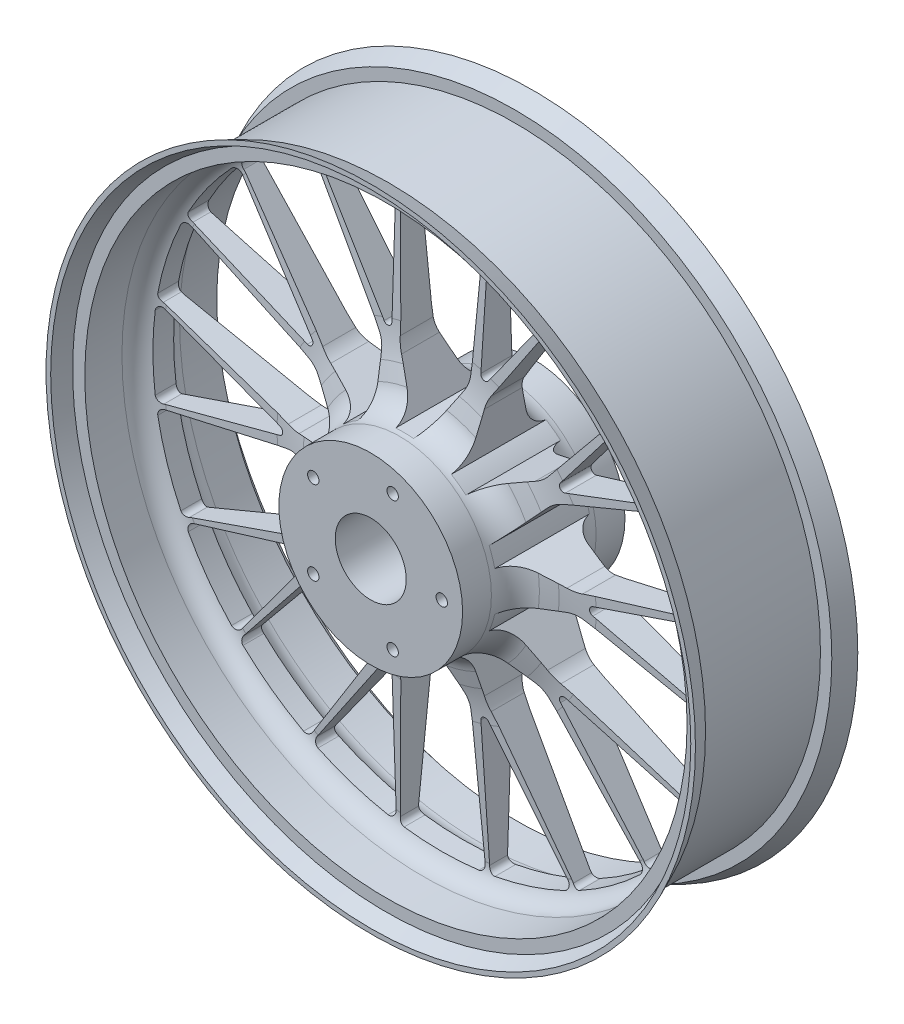
SolidWorks part; units mm, degrees
material "7050-T7651"
ref_plane "Front Plane" through (0, 0, 0) normal (0, 0, 1) x (1, 0, 0)
ref_plane "Top Plane" through (0, 0, 0) normal (0, 1, 0) x (1, 0, 0)
ref_plane "Right Plane" through (0, 0, 0) normal (1, 0, 0) x (0, 0, -1)
sketch "Sketch1" plane through (0, 0, 0) normal (0, 0, 1) x (1, 0, 0)
  line L0 (0, 0) -> (0, 203.2) construction
  line L1 (-29.8081, 197.311) -> (-24.756, 100.9121)
  line L2 (-22.1039, 91.9588) -> (-6.3592, 64.6882)
  line L3 (91.8613, 177.1487) -> (39.2866, 96.1908)
  line L4 (22.1039, 91.9588) -> (6.3592, 64.6882)
  line L5 (29.8081, 197.311) -> (24.756, 100.9121)
  line L6 (0, 0) -> (-75.5575, 232.5421) construction
  line L7 (-31.3013, 105.6196) -> (-32.8759, 195.8269)
  line L8 (-36.7583, 103.8465) -> (-88.471, 177.7703)
  line L9 (36.1696, 87.3886) -> (32.878, 56.0717)
  line L10 (71.9345, 61.4039) -> (43.1675, 48.596)
  line L11 (140.0918, 142.1072) -> (79.3427, 67.0884)
  line L12 (36.7583, 103.8465) -> (88.507, 177.7513)
  line L13 (31.3013, 105.6196) -> (32.9162, 195.8211)
  line L14 (0, 0) -> (119.438, 164.3923) construction
  line L15 (0, 0) -> (75.5575, 232.5421) construction
  line L16 (178.4427, 89.3216) -> (88.3231, 54.7279)
  line L17 (80.6276, 49.4389) -> (59.557, 26.0377)
  line L18 (94.2886, 7.3948) -> (63.4872, 13.9418)
  line L19 (196.8651, 32.6233) -> (103.6232, 7.6392)
  line L20 (90.7776, 62.4076) -> (176.0833, 91.7807)
  line L21 (87.405, 67.0496) -> (141.7305, 139.075)
  line L22 (0, 0) -> (193.2547, 62.7923) construction
  line L23 (0, 0) -> (197.8121, 143.7189) construction
  line L24 (196.8651, -32.6233) -> (103.6232, -7.6392)
  line L25 (94.2886, -7.3948) -> (63.4872, -13.9418)
  line L26 (80.6276, -49.4389) -> (59.557, -26.0377)
  line L27 (178.4427, -89.3216) -> (88.3231, -54.7279)
  line L28 (110.1229, -2.8689) -> (196.4017, -29.247)
  line L29 (110.1229, 2.8689) -> (196.4086, 29.2069)
  line L30 (0, 0) -> (193.2547, -62.7923) construction
  line L31 (0, 0) -> (244.5092, 0) construction
  line L32 (140.0918, -142.1072) -> (79.3427, -67.0884)
  line L33 (71.9345, -61.4039) -> (43.1675, -48.596)
  line L34 (36.1696, -87.3886) -> (32.878, -56.0717)
  line L35 (91.8613, -177.1487) -> (39.2866, -96.1908)
  line L36 (87.405, -67.0496) -> (141.7014, -139.1033)
  line L37 (90.7776, -62.4076) -> (176.0653, -91.8172)
  line L38 (0, 0) -> (119.438, -164.3923) construction
  line L39 (0, 0) -> (197.8121, -143.7189) construction
  line L40 (29.8081, -197.311) -> (24.756, -100.9121)
  line L41 (22.1039, -91.9588) -> (6.3592, -64.6882)
  line L42 (-22.1039, -91.9588) -> (-6.3592, -64.6882)
  line L43 (-29.8081, -197.311) -> (-24.756, -100.9121)
  line L44 (31.3013, -105.6196) -> (32.8759, -195.8269)
  line L45 (36.7583, -103.8465) -> (88.471, -177.7703)
  line L46 (0, 0) -> (0, -203.2) construction
  line L47 (0, 0) -> (75.5575, -232.5421) construction
  line L48 (-91.8613, -177.1487) -> (-39.2866, -96.1908)
  line L49 (-36.1696, -87.3886) -> (-32.878, -56.0717)
  line L50 (-71.9345, -61.4039) -> (-43.1675, -48.596)
  line L51 (-140.0918, -142.1072) -> (-79.3427, -67.0884)
  line L52 (-36.7583, -103.8465) -> (-88.507, -177.7513)
  line L53 (-31.3013, -105.6196) -> (-32.9162, -195.8211)
  line L54 (0, 0) -> (-119.438, -164.3923) construction
  line L55 (0, 0) -> (-75.5575, -232.5421) construction
  line L56 (-178.4427, -89.3216) -> (-88.3231, -54.7279)
  line L57 (-80.6276, -49.4389) -> (-59.557, -26.0377)
  line L58 (-94.2886, -7.3948) -> (-63.4872, -13.9418)
  line L59 (-196.8651, -32.6233) -> (-103.6232, -7.6392)
  line L60 (-90.7776, -62.4076) -> (-176.0833, -91.7807)
  line L61 (-87.405, -67.0496) -> (-141.7305, -139.075)
  line L62 (0, 0) -> (-193.2547, -62.7923) construction
  line L63 (0, 0) -> (-197.8121, -143.7189) construction
  line L64 (-196.8651, 32.6233) -> (-103.6232, 7.6392)
  line L65 (-94.2886, 7.3948) -> (-63.4872, 13.9418)
  line L66 (-80.6276, 49.4389) -> (-59.557, 26.0377)
  line L67 (-178.4427, 89.3216) -> (-88.3231, 54.7279)
  line L68 (-110.1229, 2.8689) -> (-196.4017, 29.247)
  line L69 (-110.1229, -2.8689) -> (-196.4086, -29.2069)
  line L70 (0, 0) -> (-193.2547, 62.7923) construction
  line L71 (0, 0) -> (-244.5092, 0) construction
  line L72 (-140.0918, 142.1072) -> (-79.3427, 67.0884)
  line L73 (-71.9345, 61.4039) -> (-43.1675, 48.596)
  line L74 (-36.1696, 87.3886) -> (-32.878, 56.0717)
  line L75 (-91.8613, 177.1487) -> (-39.2866, 96.1908)
  line L76 (-87.405, 67.0496) -> (-141.7014, 139.1033)
  line L77 (-90.7776, 62.4076) -> (-176.0653, 91.8172)
  line L78 (0, 0) -> (-119.438, 164.3923) construction
  line L79 (0, 0) -> (-197.8121, 143.7189) construction
  circle A0 centre (0, 0) radius 25
  arc A1 (26.3319, 201.4867) -> (-26.3319, 201.4867) centre (0, 0) ccw
  arc A2 (6.3592, 64.6882) -> (-6.3592, 64.6882) centre (0, 0) ccw
  arc A3 (-31.3013, 105.6196) -> (-33.3738, 102.7141) centre (-34.3009, 105.5673) cw
  arc A4 (-36.7583, 103.8465) -> (-33.3738, 102.7141) centre (-34.3009, 105.5673) ccw
  arc A5 (22.1039, 91.9588) -> (24.756, 100.9121) centre (4.7834, 101.9588) ccw
  arc A6 (-24.756, 100.9121) -> (-22.1039, 91.9588) centre (-4.7834, 101.9588) ccw
  arc A7 (-37.6158, 199.688) -> (-86.9041, 183.6788) centre (0, 0) ccw
  arc A8 (29.8081, 197.311) -> (26.3319, 201.4867) centre (25.8136, 197.5204) ccw
  arc A9 (-29.8081, 197.311) -> (-26.3319, 201.4867) centre (-25.8136, 197.5204) cw
  arc A10 (-32.8759, 195.8269) -> (-37.6158, 199.688) centre (-36.8753, 195.7571) ccw
  arc A11 (-88.471, 177.7703) -> (-86.9041, 183.6788) centre (-85.1934, 180.0631) cw
  arc A12 (139.7338, 147.5286) -> (97.1279, 178.4836) centre (0, 0) ccw
  arc A13 (43.1675, 48.596) -> (32.878, 56.0717) centre (0, 0) ccw
  arc A14 (36.7583, 103.8465) -> (33.3738, 102.7141) centre (34.3009, 105.5673) cw
  arc A15 (31.3013, 105.6196) -> (33.3738, 102.7141) centre (34.3009, 105.5673) ccw
  arc A16 (71.9345, 61.4039) -> (79.3427, 67.0884) centre (63.7998, 79.6748) ccw
  arc A17 (39.2866, 96.1908) -> (36.1696, 87.3886) centre (56.06, 85.2981) ccw
  arc A18 (86.9419, 183.661) -> (37.6568, 199.6803) centre (0, 0) ccw
  arc A19 (140.0918, 142.1072) -> (139.7338, 147.5286) centre (136.9832, 144.6245) ccw
  arc A20 (91.8613, 177.1487) -> (97.1279, 178.4836) centre (95.216, 174.9702) cw
  arc A21 (88.507, 177.7513) -> (86.9419, 183.661) centre (85.2304, 180.0456) ccw
  arc A22 (32.9162, 195.8211) -> (37.6568, 199.6803) centre (36.9156, 195.7495) cw
  arc A23 (199.7622, 37.2197) -> (183.4882, 87.3059) centre (0, 0) ccw
  arc A24 (63.4872, 13.9418) -> (59.557, 26.0377) centre (0, 0) ccw
  arc A25 (90.7776, 62.4076) -> (87.3738, 63.4808) centre (89.8009, 65.2442) cw
  arc A26 (87.405, 67.0496) -> (87.3738, 63.4808) centre (89.8009, 65.2442) ccw
  arc A27 (94.2886, 7.3948) -> (103.6232, 7.6392) centre (98.4468, 26.9577) ccw
  arc A28 (88.3231, 54.7279) -> (80.6276, 49.4389) centre (95.4905, 36.0563) ccw
  arc A29 (178.2906, 97.4817) -> (147.8341, 139.4106) centre (0, 0) ccw
  arc A30 (196.8651, 32.6233) -> (199.7622, 37.2197) centre (195.8299, 36.487) ccw
  arc A31 (178.4427, 89.3216) -> (183.4882, 87.3059) centre (179.8762, 85.5873) cw
  arc A32 (176.0833, 91.7807) -> (178.2906, 97.4817) centre (174.781, 95.5628) ccw
  arc A33 (141.7305, 139.075) -> (147.8341, 139.4106) centre (144.924, 136.6663) cw
  arc A34 (183.4882, -87.3059) -> (199.7622, -37.2197) centre (0, 0) ccw
  arc A35 (59.557, -26.0377) -> (63.4872, -13.9418) centre (0, 0) ccw
  arc A36 (110.1229, -2.8689) -> (108, 0) centre (111, 0) cw
  arc A37 (110.1229, 2.8689) -> (108, 0) centre (111, 0) ccw
  arc A38 (80.6276, -49.4389) -> (88.3231, -54.7279) centre (95.4905, -36.0563) ccw
  arc A39 (103.6232, -7.6392) -> (94.2886, -7.3948) centre (98.4468, -26.9577) ccw
  arc A40 (201.5385, -25.9323) -> (201.5438, 25.8908) centre (0, 0) ccw
  arc A41 (178.4427, -89.3216) -> (183.4882, -87.3059) centre (179.8762, -85.5873) ccw
  arc A42 (196.8651, -32.6233) -> (199.7622, -37.2197) centre (195.8299, -36.487) cw
  arc A43 (196.4017, -29.247) -> (201.5385, -25.9323) centre (197.5712, -25.4218) ccw
  arc A44 (196.4086, 29.2069) -> (201.5438, 25.8908) centre (197.5764, 25.3812) cw
  arc A45 (97.1279, -178.4836) -> (139.7338, -147.5286) centre (0, 0) ccw
  arc A46 (32.878, -56.0717) -> (43.1675, -48.596) centre (0, 0) ccw
  arc A47 (87.405, -67.0496) -> (87.3738, -63.4808) centre (89.8009, -65.2442) cw
  arc A48 (90.7776, -62.4076) -> (87.3738, -63.4808) centre (89.8009, -65.2442) ccw
  arc A49 (36.1696, -87.3886) -> (39.2866, -96.1908) centre (56.06, -85.2981) ccw
  arc A50 (79.3427, -67.0884) -> (71.9345, -61.4039) centre (63.7998, -79.6748) ccw
  arc A51 (147.8055, -139.441) -> (178.2706, -97.5184) centre (0, 0) ccw
  arc A52 (91.8613, -177.1487) -> (97.1279, -178.4836) centre (95.216, -174.9702) ccw
  arc A53 (140.0918, -142.1072) -> (139.7338, -147.5286) centre (136.9832, -144.6245) cw
  arc A54 (141.7014, -139.1033) -> (147.8055, -139.441) centre (144.8959, -136.6961) ccw
  arc A55 (176.0653, -91.8172) -> (178.2706, -97.5184) centre (174.7613, -95.5987) cw
  arc A56 (-26.3319, -201.4867) -> (26.3319, -201.4867) centre (0, 0) ccw
  arc A57 (-6.3592, -64.6882) -> (6.3592, -64.6882) centre (0, 0) ccw
  arc A58 (31.3013, -105.6196) -> (33.3738, -102.7141) centre (34.3009, -105.5673) cw
  arc A59 (36.7583, -103.8465) -> (33.3738, -102.7141) centre (34.3009, -105.5673) ccw
  arc A60 (-22.1039, -91.9588) -> (-24.756, -100.9121) centre (-4.7834, -101.9588) ccw
  arc A61 (24.756, -100.9121) -> (22.1039, -91.9588) centre (4.7834, -101.9588) ccw
  arc A62 (37.6158, -199.688) -> (86.9041, -183.6788) centre (0, 0) ccw
  arc A63 (-29.8081, -197.311) -> (-26.3319, -201.4867) centre (-25.8136, -197.5204) ccw
  arc A64 (29.8081, -197.311) -> (26.3319, -201.4867) centre (25.8136, -197.5204) cw
  arc A65 (32.8759, -195.8269) -> (37.6158, -199.688) centre (36.8753, -195.7571) ccw
  arc A66 (88.471, -177.7703) -> (86.9041, -183.6788) centre (85.1934, -180.0631) cw
  arc A67 (-139.7338, -147.5286) -> (-97.1279, -178.4836) centre (0, 0) ccw
  arc A68 (-43.1675, -48.596) -> (-32.878, -56.0717) centre (0, 0) ccw
  arc A69 (-36.7583, -103.8465) -> (-33.3738, -102.7141) centre (-34.3009, -105.5673) cw
  arc A70 (-31.3013, -105.6196) -> (-33.3738, -102.7141) centre (-34.3009, -105.5673) ccw
  arc A71 (-71.9345, -61.4039) -> (-79.3427, -67.0884) centre (-63.7998, -79.6748) ccw
  arc A72 (-39.2866, -96.1908) -> (-36.1696, -87.3886) centre (-56.06, -85.2981) ccw
  arc A73 (-86.9419, -183.661) -> (-37.6568, -199.6803) centre (0, 0) ccw
  arc A74 (-140.0918, -142.1072) -> (-139.7338, -147.5286) centre (-136.9832, -144.6245) ccw
  arc A75 (-91.8613, -177.1487) -> (-97.1279, -178.4836) centre (-95.216, -174.9702) cw
  arc A76 (-88.507, -177.7513) -> (-86.9419, -183.661) centre (-85.2304, -180.0456) ccw
  arc A77 (-32.9162, -195.8211) -> (-37.6568, -199.6803) centre (-36.9156, -195.7495) cw
  arc A78 (-199.7622, -37.2197) -> (-183.4882, -87.3059) centre (0, 0) ccw
  arc A79 (-63.4872, -13.9418) -> (-59.557, -26.0377) centre (0, 0) ccw
  arc A80 (-90.7776, -62.4076) -> (-87.3738, -63.4808) centre (-89.8009, -65.2442) cw
  arc A81 (-87.405, -67.0496) -> (-87.3738, -63.4808) centre (-89.8009, -65.2442) ccw
  arc A82 (-94.2886, -7.3948) -> (-103.6232, -7.6392) centre (-98.4468, -26.9577) ccw
  arc A83 (-88.3231, -54.7279) -> (-80.6276, -49.4389) centre (-95.4905, -36.0563) ccw
  arc A84 (-178.2906, -97.4817) -> (-147.8341, -139.4106) centre (0, 0) ccw
  arc A85 (-196.8651, -32.6233) -> (-199.7622, -37.2197) centre (-195.8299, -36.487) ccw
  arc A86 (-178.4427, -89.3216) -> (-183.4882, -87.3059) centre (-179.8762, -85.5873) cw
  arc A87 (-176.0833, -91.7807) -> (-178.2906, -97.4817) centre (-174.781, -95.5628) ccw
  arc A88 (-141.7305, -139.075) -> (-147.8341, -139.4106) centre (-144.924, -136.6663) cw
  arc A89 (-183.4882, 87.3059) -> (-199.7622, 37.2197) centre (0, 0) ccw
  arc A90 (-59.557, 26.0377) -> (-63.4872, 13.9418) centre (0, 0) ccw
  arc A91 (-110.1229, 2.8689) -> (-108, 0) centre (-111, 0) cw
  arc A92 (-110.1229, -2.8689) -> (-108, 0) centre (-111, 0) ccw
  arc A93 (-80.6276, 49.4389) -> (-88.3231, 54.7279) centre (-95.4905, 36.0563) ccw
  arc A94 (-103.6232, 7.6392) -> (-94.2886, 7.3948) centre (-98.4468, 26.9577) ccw
  arc A95 (-201.5385, 25.9323) -> (-201.5438, -25.8908) centre (0, 0) ccw
  arc A96 (-178.4427, 89.3216) -> (-183.4882, 87.3059) centre (-179.8762, 85.5873) ccw
  arc A97 (-196.8651, 32.6233) -> (-199.7622, 37.2197) centre (-195.8299, 36.487) cw
  arc A98 (-196.4017, 29.247) -> (-201.5385, 25.9323) centre (-197.5712, 25.4218) ccw
  arc A99 (-196.4086, -29.2069) -> (-201.5438, -25.8908) centre (-197.5764, -25.3812) cw
  arc A100 (-97.1279, 178.4836) -> (-139.7338, 147.5286) centre (0, 0) ccw
  arc A101 (-32.878, 56.0717) -> (-43.1675, 48.596) centre (0, 0) ccw
  arc A102 (-87.405, 67.0496) -> (-87.3738, 63.4808) centre (-89.8009, 65.2442) cw
  arc A103 (-90.7776, 62.4076) -> (-87.3738, 63.4808) centre (-89.8009, 65.2442) ccw
  arc A104 (-36.1696, 87.3886) -> (-39.2866, 96.1908) centre (-56.06, 85.2981) ccw
  arc A105 (-79.3427, 67.0884) -> (-71.9345, 61.4039) centre (-63.7998, 79.6748) ccw
  arc A106 (-147.8055, 139.441) -> (-178.2706, 97.5184) centre (0, 0) ccw
  arc A107 (-91.8613, 177.1487) -> (-97.1279, 178.4836) centre (-95.216, 174.9702) ccw
  arc A108 (-140.0918, 142.1072) -> (-139.7338, 147.5286) centre (-136.9832, 144.6245) cw
  arc A109 (-141.7014, 139.1033) -> (-147.8055, 139.441) centre (-144.8959, 136.6961) ccw
  arc A110 (-176.0653, 91.8172) -> (-178.2706, 97.5184) centre (-174.7613, 95.5987) cw
  circle A111 centre (0, 0) radius 228.6
  circle A112 centre (0, 0) radius 50 construction
  circle A113 centre (15.4508, 47.5528) radius 4
  circle A114 centre (50, 0) radius 4
  circle A115 centre (15.4508, -47.5528) radius 4
  circle A116 centre (-40.4508, -29.3893) radius 4
  circle A117 centre (-40.4508, 29.3893) radius 4
  point P11 (0, 53.8255)
  point P23 (24.5047, 96.1171)
  point P26 (-24.5047, 96.1171)
  point P27 (30, 200.9732)
  point P30 (-30, 200.9732)
  point P33 (-33, 200.5025)
  point P36 (-91.1548, 181.6068)
  point P48 (31.6378, 43.5457)
  point P77 (51.1911, 16.633)
  point P106 (51.1911, -16.633)
  point P135 (31.6378, -43.5457)
  point P164 (0, -53.8255)
  point P193 (-31.6378, -43.5457)
  point P222 (-51.1911, -16.633)
  point P251 (-51.1911, 16.633)
  point P280 (-31.6378, 43.5457)
  dimension "D1" = 50
  dimension "D2" = 406.4
  dimension "D3" = 130
  dimension "D11" = 3
  dimension "D12" = 20
  dimension "D13" = 4
  dimension "D15" = 457.2
  dimension "D16" = 100
  dimension "D17" = 8
  dimension "D19" = 108
  dimension "D4" = 6
  dimension "D5" = 105
  dimension "D6" = 60
  dimension "D7" = 3
  dimension "D8" = 18
  dimension "D9" = 30
  dimension "D10" = 2
  dimension "D14" = 10
  dimension "D18" = 5
extrude "Boss-Extrude1" add sketch "Sketch1" along normal mid plane 114.3
sketch "Sketch2" plane through (0, 0, 0) normal (1, 0, 0) x (0, 0, -1)
  line L0 (0, 0) -> (0, 217.623) construction
  line L1 (-6.35, 197.311) -> (-10.8058, 112.2901)
  line L2 (-57.15, 100.9121) -> (57.15, 100.9121) construction
  line L3 (-57.15, 228.6) -> (57.15, 228.6)
  line L4 (-57.15, 197.311) -> (57.15, 197.311) construction
  line L5 (-46.45, 212) -> (-20.2893, 212)
  line L6 (-57.15, 228.6) -> (-57.15, -228.6) construction
  line L8 (-14.5425, 89.9599) -> (-17.6349, 79.1754)
  line L9 (-57.15, 64.6882) -> (57.15, 64.6882) construction
  line L10 (-36.8602, 64.6882) -> (-57.15, 64.6882)
  line L11 (-57.15, 64.6882) -> (-57.15, 225.3213)
  line L12 (46.45, 220.6032) -> (46.45, 212)
  line L13 (36.8602, 64.6882) -> (57.15, 64.6882)
  line L14 (14.5425, 89.9599) -> (17.6349, 79.1754)
  line L15 (57.15, 225.3213) -> (46.45, 220.6032)
  line L16 (6.35, 197.311) -> (10.8058, 112.2901)
  line L17 (0, 0) -> (30.7585, 0) construction
  line L18 (-44.45, 215) -> (44.45, 215)
  line L20 (-44.45, 215) -> (-44.45, 223)
  line L21 (-44.45, 223) -> (-57.15, 228.6)
  line L22 (-57.15, 225.3213) -> (-46.45, 220.6032)
  line L23 (-46.45, 220.6032) -> (-46.45, 212)
  line L24 (44.45, 223) -> (57.15, 228.6)
  line L25 (44.45, 215) -> (44.45, 223)
  line L26 (57.15, 64.6882) -> (57.15, 225.3213)
  line L27 (46.45, 212) -> (20.2893, 212)
  arc A0 (-20.2893, 212) -> (-6.35, 197.311) centre (-20.2893, 198.0416) cw
  arc A1 (20.2893, 212) -> (6.35, 197.311) centre (20.2893, 198.0416) ccw
  arc A2 (36.8602, 64.6882) -> (17.6349, 79.1754) centre (36.8602, 84.6882) cw
  arc A3 (-17.6349, 79.1754) -> (-36.8602, 64.6882) centre (-36.8602, 84.6882) cw
  arc A4 (14.5425, 89.9599) -> (10.8058, 112.2901) centre (110.6687, 117.5237) cw
  arc A5 (-10.8058, 112.2901) -> (-14.5425, 89.9599) centre (-110.6687, 117.5237) cw
  point P5 (0, 228.6)
  point P31 (21.7891, 64.6882)
  point P34 (-21.7891, 64.6882)
  point P37 (11.4021, 100.9121)
  point P40 (-11.4021, 100.9121)
  point P45 (0, 215)
  dimension "D5" = 20
  dimension "D6" = 100
  dimension "D1" = 3
  dimension "D2" = 12.7
  dimension "D3" = 212
  dimension "D4" = 16
  dimension "D7" = 88.9
  dimension "D8" = 3
  dimension "D9" = 228.6
  dimension "D10" = 3
  dimension "D11" = 2
  dimension "D13" = 8
revolve "Cut-Revolve1" cut sketch "Sketch2" angle 360 about L17
